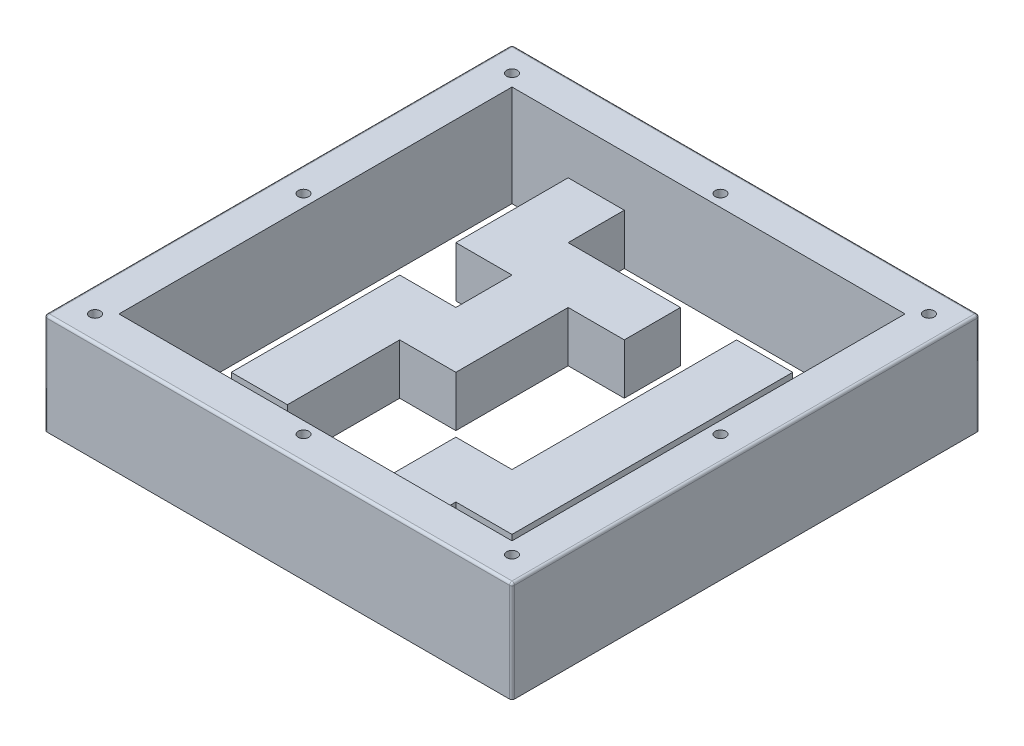
SolidWorks part; units mm, degrees
ref_plane "Plan de face" through (0, 0, 0) normal (0, 0, 1) x (1, 0, 0)
ref_plane "Plan de dessus" through (0, 0, 0) normal (0, 1, 0) x (1, 0, 0)
ref_plane "Plan de droite" through (0, 0, 0) normal (1, 0, 0) x (0, 0, -1)
sketch "Esquisse2" plane through (0, 0, 0) normal (0, 1, 0) x (1, 0, 0)
  line L1 (-92.5, 92.5) -> (92.5, 92.5)
  line L2 (-92.5, 92.5) -> (-92.5, -92.5)
  line L3 (-92.5, -92.5) -> (92.5, -92.5)
  line L4 (92.5, 92.5) -> (92.5, -92.5)
  dimension "D1" = 185
  dimension "D2" = 185
  dimension "D3" = 92.5
  dimension "D4" = 92.5
extrude "Boss.-Extru.1" add sketch "Esquisse2" against normal blind 3
sketch "Esquisse3" plane through (0, 0, 0) normal (0, 1, 0) x (1, 0, 0)
  line L0 (-77.77, 77.77) -> (77.77, 77.77)
  line L1 (-92.5, 92.5) -> (92.5, 92.5)
  line L2 (-92.5, 92.5) -> (-92.5, -92.5)
  line L3 (-92.5, -92.5) -> (92.5, -92.5)
  line L4 (92.5, 92.5) -> (92.5, -92.5)
  line L8 (77.77, 77.77) -> (77.77, -77.77)
  line L9 (-77.77, -77.77) -> (77.77, -77.77)
  line L10 (-77.77, 77.77) -> (-77.77, -77.77)
  dimension "D2" = 155.54
  dimension "D3" = 155.54
  dimension "D1" = 14.73
extrude "Boss.-Extru.2" add sketch "Esquisse3" along normal blind 40
sketch "Esquisse4" plane through (0, 0, 0) normal (0, 1, 0) x (1, 0, 0)
  line L0 (-55.55, 77.77) -> (-33.33, 77.77)
  line L1 (77.77, 77.77) -> (-77.77, 77.77) construction
  line L2 (-33.33, 77.77) -> (-33.33, 55.55)
  line L3 (-33.33, 55.55) -> (11.11, 55.55)
  line L4 (11.11, 55.55) -> (11.11, 33.33)
  line L5 (11.11, 33.33) -> (-11.11, 33.33)
  line L6 (-11.11, 33.33) -> (-11.11, -11.11)
  line L8 (-33.33, -11.11) -> (-33.33, -55.55)
  line L9 (-33.33, -55.55) -> (-55.55, -55.55)
  line L13 (-33.33, -11.11) -> (-11.11, -11.11)
  line L14 (-55.55, 77.77) -> (-55.55, 33.33)
  line L15 (-55.55, 33.33) -> (-33.33, 33.33)
  line L16 (-33.33, 33.33) -> (-33.33, 11.11)
  line L17 (-33.33, 11.11) -> (-55.55, 11.11)
  line L18 (-55.55, 11.11) -> (-55.55, -55.55)
  line L19 (-77.77, 77.77) -> (-77.77, -77.77) construction
  line L20 (-77.77, -77.77) -> (77.77, -77.77) construction
  line L21 (77.77, -77.77) -> (77.77, 77.77) construction
  line L22 (33.33, 55.55) -> (55.55, 55.55)
  line L23 (33.33, 55.55) -> (33.33, -33.33)
  line L25 (55.55, 55.55) -> (55.55, -55.55)
  line L28 (55.55, -55.55) -> (33.33, -55.55)
  line L30 (33.33, -33.33) -> (11.11, -33.33)
  line L32 (33.33, -77.77) -> (11.11, -77.77)
  line L33 (11.11, -33.33) -> (11.11, -77.77)
  line L34 (33.33, -55.55) -> (33.33, -77.77)
  line L35 (77.77, -77.77) -> (77.77, 77.77) construction
  dimension "D1" = 22.22
  dimension "D2" = 22.22
  dimension "D3" = 22.22
  dimension "D4" = 22.22
  dimension "D5" = 22.22
  dimension "D6" = 22.22
  dimension "D7" = 22.22
  dimension "D8" = 22.22
  dimension "D9" = 22.22
  dimension "D10" = 66.66
  dimension "D11" = 22.22
  dimension "D12" = 22.22
  dimension "D13" = 22.22
  dimension "D14" = 22.22
  dimension "D15" = 22.22
  dimension "D16" = 22.22
  dimension "D17" = 22.22
  dimension "D18" = 44.44
extrude "Boss.-Extru.3" add sketch "Esquisse4" along normal blind 20
sketch "Esquisse5" plane through (0, 0, 0) normal (0, 1, 0) x (1, 0, 0)
  line L0 (77.77, 77.77) -> (-33.33, 77.77) construction
  line L1 (-33.33, 55.55) -> (-11.11, 55.55)
  line L2 (-33.33, 55.55) -> (-33.33, 77.77)
  line L3 (-33.33, 77.77) -> (-11.11, 77.77)
  line L4 (-11.11, 55.55) -> (-11.11, 77.77)
  line L5 (-11.11, -11.11) -> (-11.11, 33.33) construction
  line L6 (-11.11, 33.33) -> (11.11, 33.33)
  line L7 (-11.11, 33.33) -> (-11.11, 11.11)
  line L8 (-11.11, 11.11) -> (11.11, 11.11)
  line L9 (11.11, 33.33) -> (11.11, 11.11)
  line L10 (11.11, 33.33) -> (11.11, 55.55) construction
  line L11 (-33.33, 11.11) -> (-55.55, 11.11) construction
  line L12 (33.33, -55.55) -> (55.55, -55.55) construction
  line L13 (-33.33, -11.11) -> (-20.98, -11.11)
  line L14 (-33.33, -11.11) -> (-33.33, -23.46)
  line L15 (-33.33, -23.46) -> (-20.98, -23.46)
  line L16 (-20.98, -11.11) -> (-20.98, -23.46)
  line L17 (-72.835, 28.395) -> (-60.485, 28.395)
  line L18 (-72.835, 28.395) -> (-72.835, 16.045)
  line L19 (-72.835, 16.045) -> (-60.485, 16.045)
  line L20 (-60.485, 28.395) -> (-60.485, 16.045)
  line L21 (-72.835, -60.485) -> (-60.485, -60.485)
  line L22 (-72.835, -60.485) -> (-72.835, -72.835)
  line L23 (-72.835, -72.835) -> (-60.485, -72.835)
  line L24 (-60.485, -60.485) -> (-60.485, -72.835)
  line L25 (60.485, -60.485) -> (72.835, -60.485)
  line L26 (60.485, -60.485) -> (60.485, -72.835)
  line L27 (60.485, -72.835) -> (72.835, -72.835)
  line L28 (72.835, -60.485) -> (72.835, -72.835)
  line L29 (11.11, -55.55) -> (-1.24, -55.55)
  line L30 (11.11, -55.55) -> (11.11, -43.2)
  line L31 (11.11, -43.2) -> (-1.24, -43.2)
  line L32 (-1.24, -55.55) -> (-1.24, -43.2)
  line L34 (11.11, -33.33) -> (11.11, -77.77) construction
  line L35 (-77.77, 77.77) -> (-77.77, -77.77) construction
  line L36 (-55.55, 33.33) -> (-33.33, 33.33) construction
  line L37 (-55.55, 77.77) -> (-55.55, 33.33) construction
  line L38 (-77.77, -77.77) -> (11.11, -77.77) construction
  line L39 (77.77, -77.77) -> (77.77, 77.77) construction
  dimension "D1" = 12.35
  dimension "D2" = 12.35
  dimension "D3" = 12.35
  dimension "D4" = 12.35
  dimension "D5" = 12.35
  dimension "D6" = 12.35
  dimension "D7" = 12.35
  dimension "D8" = 12.35
  dimension "D9" = 12.35
  dimension "D10" = 12.35
  dimension "D11" = 4.935
  dimension "D12" = 4.935
  dimension "D13" = 4.935
  dimension "D14" = 4.935
  dimension "D15" = 4.935
  dimension "D16" = 4.935
extrude "Enlèv. mat.-Extru.1" cut sketch "Esquisse5" against normal up to next
fillet "Congé1" radius 1 8 edges at (-92.5, 18.5, -92.5) (-92.5, 18.5, 92.5) (-92.5, 40, 0) (0, 40, 92.5) (0, 40, -92.5) (92.5, 40, 0) (92.5, 18.5, -92.5) (92.5, 18.5, 92.5)
sketch "Esquisse6" plane through (0, 40, 0) normal (0, 1, 0) x (1, 0, 0)
  line L0 (92.5, 91.5) -> (92.5, -91.5) construction
  line L1 (-91.5, 92.5) -> (91.5, 92.5) construction
  line L2 (91.5, -92.5) -> (-91.5, -92.5) construction
  line L3 (-92.5, -91.5) -> (-92.5, 91.5) construction
  circle A0 centre (-82.5, -82.5) radius 1.1
  circle A1 centre (82.5, -82.5) radius 1.1
  circle A2 centre (82.5, 82.5) radius 1.1
  circle A3 centre (-82.5, 82.5) radius 1.1
  circle A4 centre (0, 82.5) radius 1.1
  circle A5 centre (82.5, 0) radius 1.1
  circle A6 centre (-82.5, 0) radius 1.1
  circle A7 centre (0, -82.5) radius 1.1
  dimension "D1" = 2.2
  dimension "D2" = 10
  dimension "D3" = 10
  dimension "D4" = 10
  dimension "D5" = 10
  dimension "D6" = 82.5
  dimension "D7" = 82.5
  dimension "D8" = 82.5
extrude "Enlèv. mat.-Extru.2" cut sketch "Esquisse6" against normal through all
sketch "Esquisse7" plane through (0, 40, 0) normal (0, 1, 0) x (1, 0, 0)
  circle A0 centre (-82.5, -82.5) radius 2.1
  circle A1 centre (-82.5, 82.5) radius 2.1
  circle A2 centre (82.5, 82.5) radius 2.1
  circle A3 centre (82.5, -82.5) radius 2.1
  dimension "D1" = 4.2
extrude "Enlèv. mat.-Extru.3" cut sketch "Esquisse7" against normal through all
sketch "Esquisse8" plane through (0, 0, 92.5) normal (0, 0, 1) x (1, 0, 0)
  line L0 (-91.5, -3) -> (91.5, -3) construction
  line L1 (114.072, -20.4095) -> (-112.4133, -20.4095)
  line L2 (114.072, -20.4095) -> (114.072, 0)
  line L3 (114.072, 0) -> (-112.4133, 0)
  line L4 (-112.4133, -20.4095) -> (-112.4133, 0)
  dimension "D1" = 3
extrude "Enlèv. mat.-Extru.4" cut sketch "Esquisse8" against normal through all
sketch "Esquisse9" plane through (0, 40, 0) normal (0, 1, 0) x (1, 0, 0)
  circle A2 centre (0, 82.5) radius 2.1
  circle A3 centre (82.5, 0) radius 2.1
  circle A4 centre (0, -82.5) radius 2.1
  circle A5 centre (-82.5, 0) radius 2.1
  dimension "D1" = 4.2
extrude "Enlèv. mat.-Extru.5" cut sketch "Esquisse9" against normal blind 37
